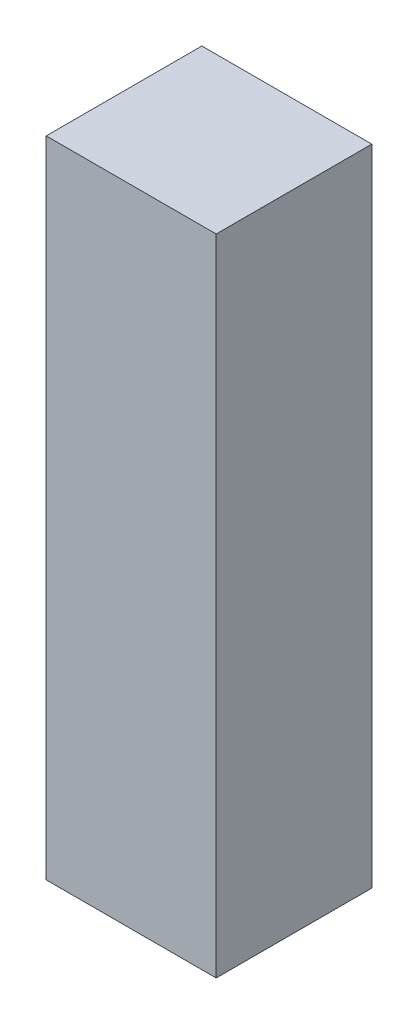
SolidWorks part; units mm, degrees
ref_plane "Front Plane" through (0, 0, 0) normal (0, 0, 1) x (1, 0, 0)
ref_plane "Top Plane" through (0, 0, 0) normal (0, 1, 0) x (1, 0, 0)
ref_plane "Right Plane" through (0, 0, 0) normal (1, 0, 0) x (0, 0, -1)
sketch "Sketch1" plane through (0, 0, 0) normal (0, 1, 0) x (1, 0, 0)
  line L5 (13.65, -12.5) -> (-13.65, -12.5)
  line L6 (13.65, -12.5) -> (13.65, 12.5)
  line L7 (13.65, 12.5) -> (-13.65, 12.5)
  line L8 (-13.65, -12.5) -> (-13.65, 12.5)
  line L9 (13.65, -12.5) -> (-13.65, 12.5) construction
  line L10 (13.65, 12.5) -> (-13.65, -12.5) construction
  point P0 (0, 0)
  dimension "D1" = 27.3
  dimension "D2" = 25
extrude "Boss-Extrude1" add sketch "Sketch1" along normal blind 103.5
